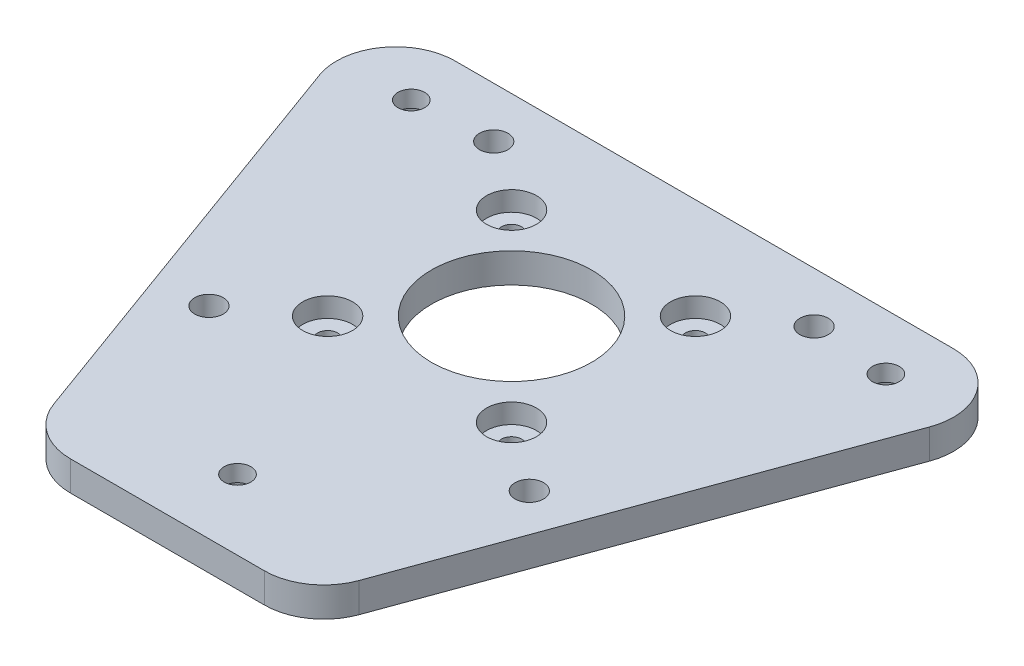
SolidWorks part; units mm, degrees
ref_plane "Front Plane" through (0, 0, 0) normal (0, 0, 1) x (1, 0, 0)
ref_plane "Top Plane" through (0, 0, 0) normal (0, 1, 0) x (1, 0, 0)
ref_plane "Right Plane" through (0, 0, 0) normal (1, 0, 0) x (0, 0, -1)
sketch "Sketch2" plane through (0, 0, 0) normal (0, 1, 0) x (1, 0, 0)
  line L1 (-65, -65) -> (65, -65)
  line L2 (-65, -65) -> (-65, 65)
  line L3 (-65, 65) -> (65, 65)
  line L4 (65, -65) -> (65, 65)
  line L5 (-65, -65) -> (65, 65) construction
  line L6 (-65, 65) -> (65, -65) construction
  point P0 (0, 0)
  dimension "D1" = 130
  dimension "D2" = 130
extrude "Boss-Extrude1" add sketch "Sketch2" along normal blind 5
ref_plane "Plane1" through (0, 5, 0) normal (0, 1, 0) x (1, 0, 0)
sketch "Sketch3" plane through (0, 5, 0) normal (0, 1, 0) x (1, 0, 0)
  line L0 (0, 0) -> (0, 15.5) construction
  line L1 (0, 15.5) -> (-15.5, 15.5) construction
  line L2 (0, 0) -> (-27, 0) construction
  line L3 (0, 0) -> (0, -24) construction
  circle A0 centre (0, 0) radius 13.5
  point P17 (-27, -24)
  point P18 (27, -24)
  point P25 (15.5, -15.5)
  point P26 (-15.5, -15.5)
  point P27 (-15.5, 15.5)
  point P28 (-27, 24)
  point P29 (27, 24)
  point P30 (15.5, 15.5)
  dimension "D1" = 27
  dimension "D4" = 15.5
  dimension "D9" = 15.5
  dimension "D2" = 15.5
  dimension "D3" = 15.5
  dimension "D6" = 27
  dimension "D7" = 54
  dimension "D8" = 24
  dimension "D5" = 48
  dimension "D10" = 27
  dimension "D11" = 24
extrude "Cut-Extrude1" cut sketch "Sketch3" against normal blind 5
ref_plane "Plane3" through (0, 5, 0) normal (0, 1, 0) x (1, 0, 0)
sketch "Sketch5" plane through (0, 0, 0) normal (0, 1, 0) x (1, 0, 0)
  line L0 (0, 0) -> (-40, 0) construction
  line L1 (-40, 0) -> (-40, 23.1) construction
  line L2 (0, 0) -> (0, -18.9982) construction
  point P11 (0, -46.19)
  point P12 (-40, 23.1)
  point P13 (40, 23.1)
  dimension "D3" = 46.19
  dimension "D1" = 23.1
  dimension "D2" = 40
  dimension "D4" = 40
ref_plane "Plane6" through (0, 5, 0) normal (0, 1, 0) x (1, 0, 0)
sketch "Sketch8" plane through (0, 5, 0) normal (0, 1, 0) x (1, 0, 0)
  line L0 (0, 0) -> (0, 30.6481) construction
  line L1 (0, 0) -> (56.2917, 32.5) construction
  line L2 (0, 0) -> (37.3839, 0) construction
  line L3 (0, 0) -> (-56.2917, 32.5) construction
  line L4 (0, 0) -> (0, -58) construction
  line L5 (-42.0098, 32.5) -> (42.0098, 32.5)
  line L6 (51.4067, 19.0796) -> (25.7449, -51.4204)
  line L7 (-51.4067, 19.0796) -> (-25.7449, -51.4204)
  line L8 (-16.3481, -58) -> (16.3481, -58)
  line L9 (-65, 65) -> (-65, -65)
  line L10 (-65, -65) -> (65, -65)
  line L11 (65, -65) -> (65, 65)
  line L12 (65, 65) -> (-65, 65)
  arc A0 (-25.7449, -51.4204) -> (-16.3481, -58) centre (-16.3481, -48) ccw
  arc A1 (25.7449, -51.4204) -> (16.3481, -58) centre (16.3481, -48) cw
  arc A2 (51.4067, 19.0796) -> (42.0098, 32.5) centre (42.0098, 22.5) ccw
  arc A3 (-51.4067, 19.0796) -> (-42.0098, 32.5) centre (-42.0098, 22.5) cw
  point P9 (0, -58)
  point P14 (-23.35, -58)
  point P17 (23.35, -58)
  dimension "D5" = 10
  dimension "D1" = 30
  dimension "D2" = 65
  dimension "D3" = 58
  dimension "D4" = 46.7
extrude "Cut-Extrude6" cut sketch "Sketch8" against normal through all
hole_wizard "M4 Clearance Hole1" positions "Sketch11" profile "Sketch12" hole size "M4" standard "ANSI Metric" end condition up to next
sketch "Sketch11" plane through (0, 5, 0) normal (0, 1, 0) x (1, 0, 0)
  point P0 (-27, 24)
  point P4 (27, 24)
  point P7 (27, -24)
  point P10 (-27, -24)
sketch "Sketch12" plane through (-27, 5, -24) normal (1, 0, 0) x (0, 0, 1)
  line L0 (0, 0) -> (0, 5)
  line L1 (0, 5) -> (2.4, 5)
  line L2 (2.4, 5) -> (2.4, 0)
  line L5 (2.4, 0) -> (0, 0)
  line L11 (0, -6.35) -> (0, 107.95) construction
  dimension "Thru Hole Dia." = 4.8
  dimension "Thru Hole Depth" = 5
hole_wizard "CBORE for M3 Hex Head Machine Screw1" positions "Sketch15" profile "Sketch16" counterbore size "M3" standard "ANSI Metric" end condition up to next
sketch "Sketch15" plane through (0, 5, 0) normal (0, 1, 0) x (1, 0, 0)
  point P0 (-15.5, 15.5)
  point P3 (15.5, 15.5)
  point P6 (15.5, -15.5)
  point P9 (-15.5, -15.5)
sketch "Sketch16" plane through (-15.5, 5, -15.5) normal (1, 0, 0) x (0, 0, 1)
  line L0 (0, 0) -> (0, 5)
  line L1 (0, 5) -> (1.7, 5)
  line L3 (1.7, 5) -> (1.7, 3.3)
  line L4 (1.7, 3.3) -> (4.2, 3.3)
  line L5 (4.2, 3.3) -> (4.2, 0)
  line L7 (4.2, 0) -> (0, 0)
  line L11 (0, -6.35) -> (0, 107.95) construction
  dimension "Thru Hole Dia." = 3.4
  dimension "Thru Hole Depth" = 5
  dimension "C'Bore Dia." = 8.4
  dimension "C'Bore Depth" = 3.3
hole_wizard "CBORE for M4 SBHCS1" positions "Sketch18" profile "Sketch19" counterbore size "M4" standard "ANSI Metric" end condition up to next
sketch "Sketch18" plane through (0, 0, 0) normal (0, -1, 0) x (-1, 0, 0)
  point P0 (0, -46.19)
  point P3 (40, 23.1)
  point P6 (-40, 23.1)
sketch "Sketch19" plane through (0, 0, 46.19) normal (1, 0, 0) x (0, 0, -1)
  line L0 (0, 0) -> (0, 5)
  line L1 (0, 5) -> (2.25, 5)
  line L3 (2.25, 5) -> (2.25, 2.2)
  line L4 (2.25, 2.2) -> (4.3, 2.2)
  line L5 (4.3, 2.2) -> (4.3, 0)
  line L7 (4.3, 0) -> (0, 0)
  line L11 (0, -6.35) -> (0, 107.95) construction
  dimension "Thru Hole Dia." = 4.5
  dimension "Thru Hole Depth" = 5
  dimension "C'Bore Dia." = 8.6
  dimension "C'Bore Depth" = 2.2
